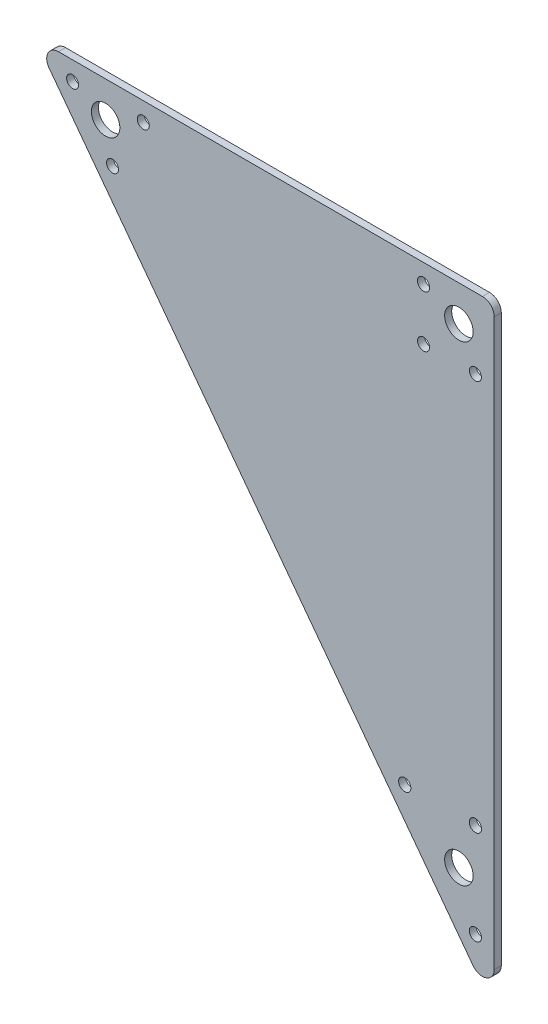
SolidWorks part; units mm, degrees
material "6061 合金"
ref_plane "前视基准面" through (0, 0, 0) normal (0, 0, 1) x (1, 0, 0)
ref_plane "上视基准面" through (0, 0, 0) normal (0, 1, 0) x (1, 0, 0)
ref_plane "右视基准面" through (0, 0, 0) normal (1, 0, 0) x (0, 0, -1)
sketch "草图2" plane through (0, 0, 0) normal (0, 0, 1) x (1, 0, 0)
  line L3 (-180, 15) -> (15, 15)
  line L4 (15, 15) -> (15, -245)
  line L6 (-180, 15) -> (15, -245)
  line L7 (-150, 0) -> (0, 0) construction
  line L8 (0, 0) -> (0, -200) construction
  line L9 (-150, 0) -> (0, -200) construction
  line L10 (-164, 7) -> (-147.0489, -15.6014) construction
  line L11 (-147.0489, -15.6014) -> (-134, 7) construction
  line L12 (-134, 7) -> (-164, 7) construction
  line L13 (-23, -181) -> (7, -221) construction
  line L14 (-15, 7) -> (7, 7) construction
  line L17 (7, 7) -> (7, -15) construction
  line L18 (7, -221) -> (7, -181) construction
  line L19 (7, -181) -> (-23, -181) construction
  line L20 (7, -15) -> (-15, -15) construction
  line L21 (-15, -15) -> (-15, 7) construction
  circle A0 centre (0, 0) radius 6.05
  circle A1 centre (-150, 0) radius 6.05
  circle A2 centre (0, -200) radius 6.05
  circle A7 centre (-164, 7) radius 2.55
  circle A8 centre (-134, 7) radius 2.55
  circle A9 centre (-147.0489, -15.6014) radius 2.55
  circle A10 centre (-15, 7) radius 2.6
  circle A12 centre (7, -15) radius 2.55
  circle A13 centre (7, -221) radius 2.6
  circle A14 centre (-23, -181) radius 2.6
  circle A15 centre (7, -181) radius 2.6
  circle A18 centre (-15, -15) radius 2.55
  dimension "D1" = 200
  dimension "D2" = 150
  dimension "D3" = 15
  dimension "D5" = 8
  dimension "D7" = 8
  dimension "D8" = 12.1
  dimension "D16" = 40
  dimension "D17" = 5.2
  dimension "D4" = 15
  dimension "D6" = 15
  dimension "D9" = 30
  dimension "D10" = 8
  dimension "D11" = 8
  dimension "D12" = 22
  dimension "D13" = 22
  dimension "D14" = 8
  dimension "D15" = 8
  dimension "D19" = 60
extrude "凸台-拉伸1" add sketch "草图2" along normal blind 3
fillet "圆角1" radius 5 3 edges at (15, -245, 1.5) (-180, 15, 1.5) (15, 15, 1.5)
